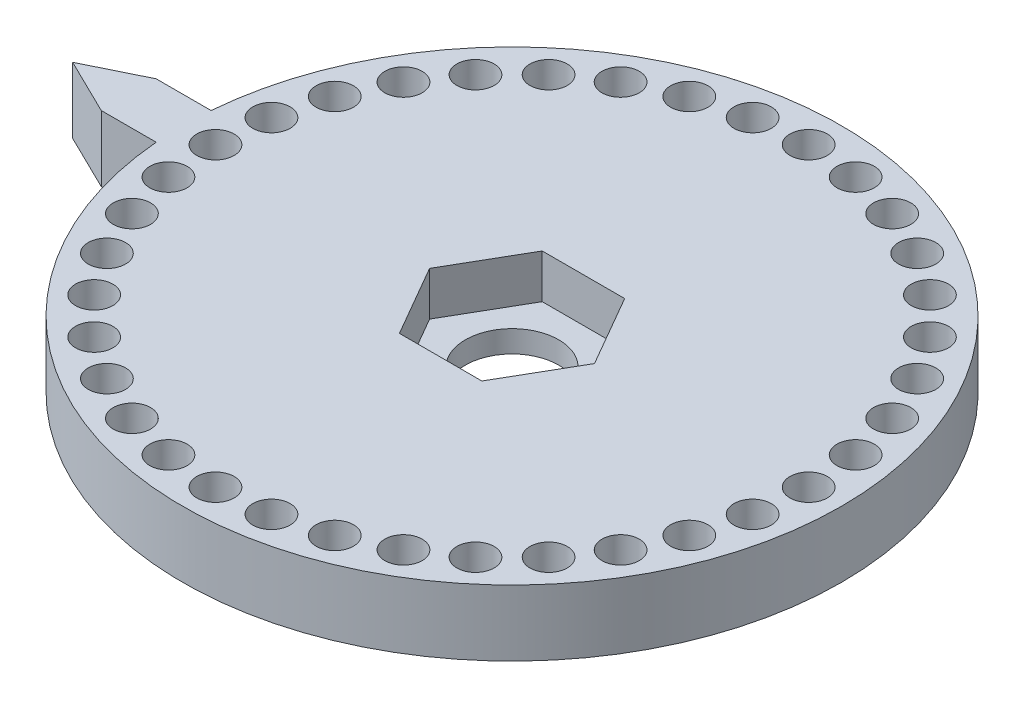
SolidWorks part; units mm, degrees
material "ABS PC"
ref_plane "Front Plane" through (0, 0, 0) normal (0, 0, 1) x (1, 0, 0)
ref_plane "Top Plane" through (0, 0, 0) normal (0, 1, 0) x (1, 0, 0)
ref_plane "Right Plane" through (0, 0, 0) normal (1, 0, 0) x (0, 0, -1)
sketch "Sketch1" plane through (0, 0, 0) normal (0, 1, 0) x (1, 0, 0)
  circle A0 centre (0, 0) radius 30
  dimension "D1" = 60
extrude "Boss-Extrude1" add sketch "Sketch1" along normal blind 6
sketch "Sketch2" plane through (0, 6, 0) normal (0, 1, 0) x (1, 0, 0)
  line L1 (3.7528, 6.5) -> (-3.7528, 6.5)
  line L2 (-3.7528, 6.5) -> (-7.5056, 0)
  line L3 (-7.5056, 0) -> (-3.7528, -6.5)
  line L4 (-3.7528, -6.5) -> (3.7528, -6.5)
  line L5 (3.7528, -6.5) -> (7.5056, 0)
  line L6 (7.5056, 0) -> (3.7528, 6.5)
  circle A0 centre (0, 0) radius 6.5 construction
  dimension "D1" = 13
extrude "Cut-Extrude1" cut sketch "Sketch2" against normal blind 4
sketch "Sketch3" plane through (0, 6, 0) normal (0, 1, 0) x (1, 0, 0)
  circle A0 centre (0, 27) radius 1.7
  point P51 (0, 0)
  dimension "D1" = 3.4
  dimension "D2" = 27
  dimension "D3" = 0
extrude "Cut-Extrude2" cut sketch "Sketch3" against normal through all
pattern_circular "CirPattern1" count 36 every 10 about axis through (0, 0, 0) along (0, 1, 0) of "Cut-Extrude2"
sketch "Sketch4" plane through (0, 2, 0) normal (0, 1, 0) x (1, 0, 0)
  circle A0 centre (0, 0) radius 4.25
  dimension "D1" = 8.5
extrude "Cut-Extrude3" cut sketch "Sketch4" against normal through all
sketch "Sketch5" plane through (0, 6, 0) normal (0, 1, 0) x (1, 0, 0)
  line L0 (-34.8957, 2.5) -> (-40, 0)
  line L1 (-29.8957, 2.5) -> (-29.8957, -2.5)
  line L2 (-40, 0) -> (-34.8957, -2.5)
  line L3 (-29.8957, 2.5) -> (-34.8957, 2.5)
  line L4 (3.7528, 6.5) -> (-3.7528, 6.5) construction
  line L7 (-29.8957, -2.5) -> (-34.8957, -2.5)
  circle A0 centre (0, 0) radius 4.25 construction
  circle A1 centre (0, 0) radius 30 construction
  dimension "D1" = 40
  dimension "D2" = 5
  dimension "D3" = 2.5
  dimension "D4" = 5
extrude "Boss-Extrude2" add sketch "Sketch5" against normal blind 6
